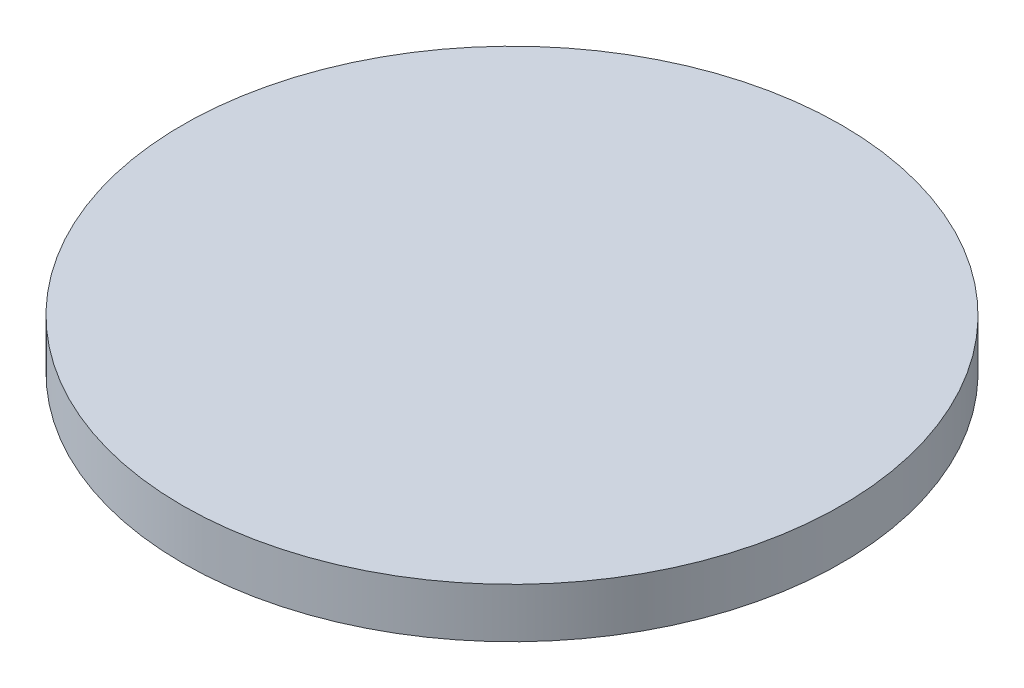
SolidWorks part; units mm, degrees
material "AISI 1045 Steel, cold drawn"
ref_plane "Front Plane" through (0, 0, 0) normal (0, 0, 1) x (1, 0, 0)
ref_plane "Top Plane" through (0, 0, 0) normal (0, 1, 0) x (1, 0, 0)
ref_plane "Right Plane" through (0, 0, 0) normal (1, 0, 0) x (0, 0, -1)
sketch "Sketch1" plane through (0, 0, 0) normal (0, 1, 0) x (1, 0, 0)
  circle A0 centre (0, 0) radius 5.3
  dimension "D1" = 10.6
extrude "Boss-Extrude1" add sketch "Sketch1" along normal blind 0.8 contours A0
